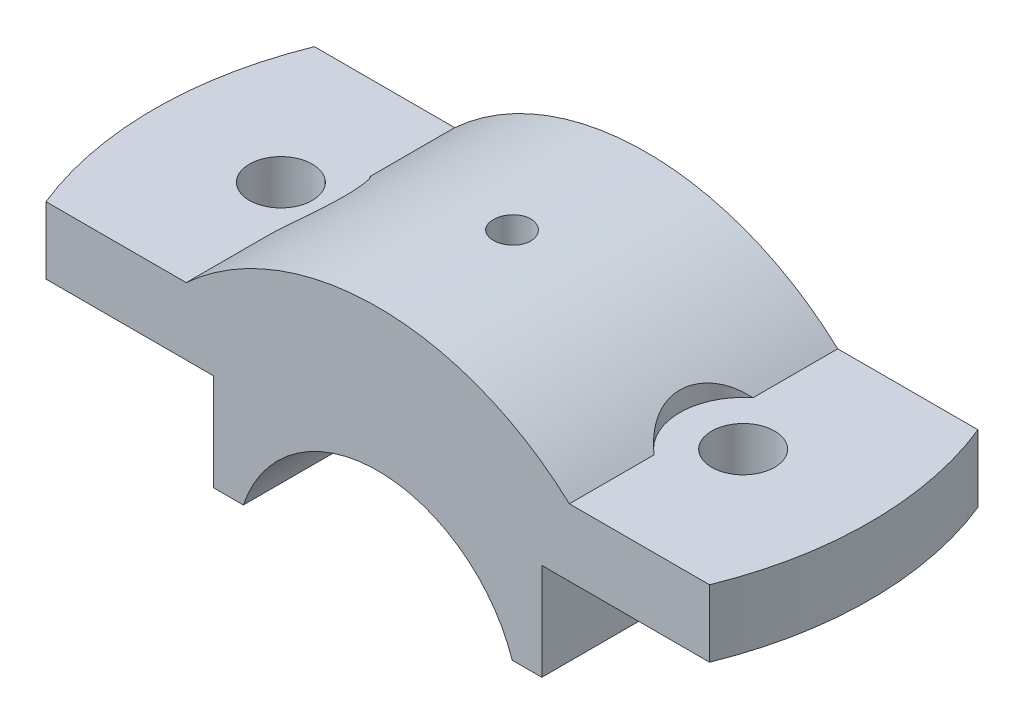
SolidWorks part; units mm, degrees
ref_plane "Front Plane" through (0, 0, 0) normal (0, 0, 1) x (1, 0, 0)
ref_plane "Top Plane" through (0, 0, 0) normal (0, 1, 0) x (1, 0, 0)
ref_plane "Right Plane" through (0, 0, 0) normal (1, 0, 0) x (0, 0, -1)
sketch "Sketch1" plane through (0, 0, 0) normal (0, 0, 1) x (1, 0, 0)
  line L0 (18.0278, 6) -> (22, 6)
  line L1 (22, 6) -> (22, 19)
  line L2 (22, 19) -> (49, 19)
  line L3 (49, 19) -> (49, 28)
  line L4 (49, 28) -> (25.6905, 28)
  line L5 (0, 0) -> (0, 45.123) construction
  line L6 (-49, 19) -> (-49, 28)
  line L7 (-22, 19) -> (-49, 19)
  line L8 (-22, 6) -> (-22, 19)
  line L9 (-18.0278, 6) -> (-22, 6)
  line L10 (-25.6905, 28) -> (-49, 28)
  arc A0 (18.0278, 6) -> (-18.0278, 6) centre (0, 0) ccw
  arc A1 (25.6905, 28) -> (-25.6905, 28) centre (0, 0) ccw
  point P11 (0, 28)
  dimension "D1" = 19
  dimension "D6" = 38
  dimension "D2" = 44
  dimension "D3" = 49
  dimension "D4" = 19
  dimension "D5" = 9
  dimension "D7" = 6
extrude "Boss-Extrude1" add sketch "Sketch1" along normal mid plane 36
sketch "Sketch2" plane through (0, 28, 0) normal (0, 1, 0) x (1, 0, 0)
  line L0 (-25.6905, 18) -> (-49, 18) construction
  line L1 (-49, -18) -> (-49, 18) construction
  line L2 (-25.6905, -18) -> (-49, -18) construction
  line L3 (-44.4972, 18) -> (-49, 18)
  line L4 (-49, -18) -> (-49, 18)
  line L5 (-44.4972, -18) -> (-49, -18)
  line L6 (0, -18) -> (0, 18) construction
  line L7 (-25.6905, -18) -> (25.6905, -18) construction
  line L8 (25.6905, 18) -> (-25.6905, 18) construction
  line L9 (44.4972, -18) -> (49, -18)
  line L10 (49, -18) -> (49, 18)
  line L11 (44.4972, 18) -> (49, 18)
  arc A0 (-44.4972, 18) -> (-44.4972, -18) centre (0, 0) ccw
  arc A1 (44.4972, 18) -> (44.4972, -18) centre (0, 0) cw
  circle A2 centre (-31, 0) radius 4.2217
  circle A3 centre (31, 0) radius 4.2217
  dimension "D1" = 48
  dimension "D2" = 62
extrude "Cut-Extrude1" cut sketch "Sketch2" against normal up to next and the other way through all
sketch "Sketch3" plane through (0, 28, 0) normal (0, 1, 0) x (1, 0, 0)
  line L0 (0, 18) -> (0, -18) construction
  line L1 (25.6905, 18) -> (-25.6905, 18) construction
  line L2 (-25.6905, -18) -> (25.6905, -18) construction
  circle A0 centre (-31, 0) radius 8.5
  circle A1 centre (31, 0) radius 8.5
  dimension "D1" = 17
extrude "Cut-Extrude2" cut sketch "Sketch3" along normal blind 36
ref_plane "Plane1" through (0, 25, 0) normal (0, 1, 0) x (1, 0, 0)
hole_wizard "M6 Tapped Hole2" positions "Sketch19" profile "Sketch18" tap size "M6" standard "ISO"
sketch "Sketch19" plane through (0, 25, 0) normal (0, 1, 0) x (1, 0, 0)
  point P0 (0, 0)
sketch "Sketch18" plane through (0, 25, 0) normal (1, 0, 0) x (0, 0, -1)
  line L0 (0, 0) -> (0, 13)
  line L1 (0, 13) -> (2.5, 13)
  line L2 (2.5, 13) -> (2.5, 0)
  line L5 (2.5, 0) -> (0, 0)
  line L11 (0, -6.35) -> (0, 107.95) construction
  dimension "Thru Tap Drill Dia." = 5
  dimension "Thru Tap Drill Depth" = 13
cosmetic thread "Hole Thread2" parameters "D2"=6
hole_wizard "M5 Tapped Hole1" positions "Sketch21" profile "Sketch20" tap size "M5" standard "ISO" end condition through all
sketch "Sketch21" plane through (0, 25, 0) normal (0, 1, 0) x (1, 0, 0)
  point P0 (0, 0)
sketch "Sketch20" plane through (0, 25, 0) normal (1, 0, 0) x (0, 0, 1)
  line L0 (0, 0) -> (0, 19)
  line L1 (0, 19) -> (2.1, 19)
  line L2 (2.1, 19) -> (2.1, 0)
  line L5 (2.1, 0) -> (0, 0)
  line L11 (0, -6.35) -> (0, 107.95) construction
  dimension "Thru Tap Drill Dia." = 4.2
  dimension "Thru Tap Drill Depth" = 19
cosmetic thread "Hole Thread3" parameters "D2"=5
